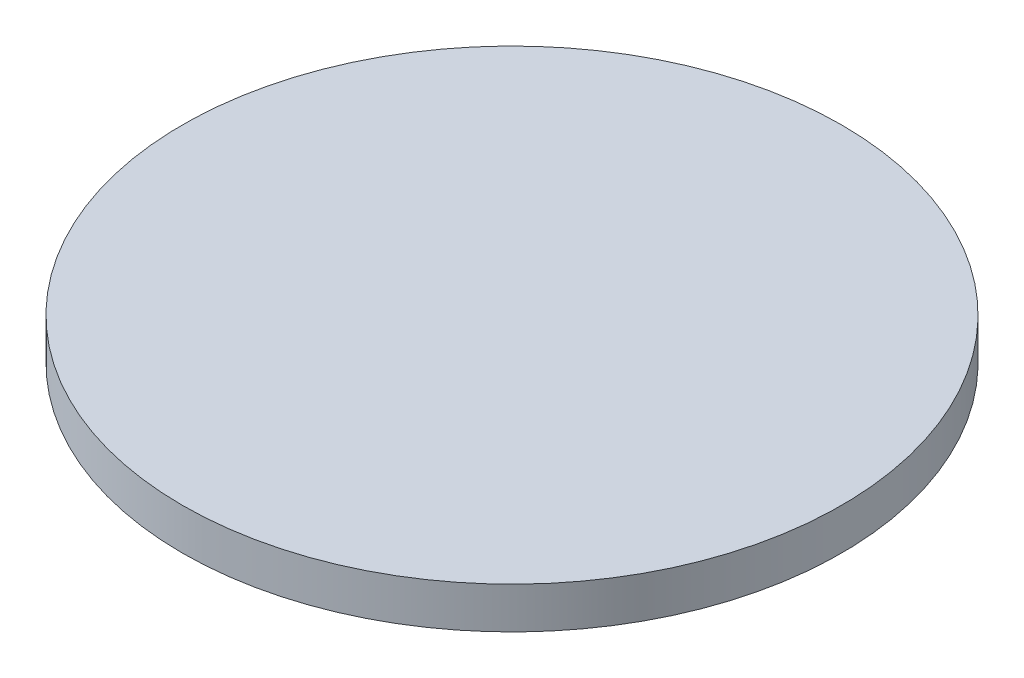
SolidWorks part; units mm, degrees
ref_plane "Front Plane" through (0, 0, 0) normal (0, 0, 1) x (1, 0, 0)
ref_plane "Top Plane" through (0, 0, 0) normal (0, 1, 0) x (1, 0, 0)
ref_plane "Right Plane" through (0, 0, 0) normal (1, 0, 0) x (0, 0, -1)
sketch "Sketch2" plane through (0, 0, 0) normal (0, 1, 0) x (1, 0, 0)
  circle A0 centre (0, 0) radius 39.818
extrude "Boss-Extrude1" add sketch "Sketch2" along normal blind 5
